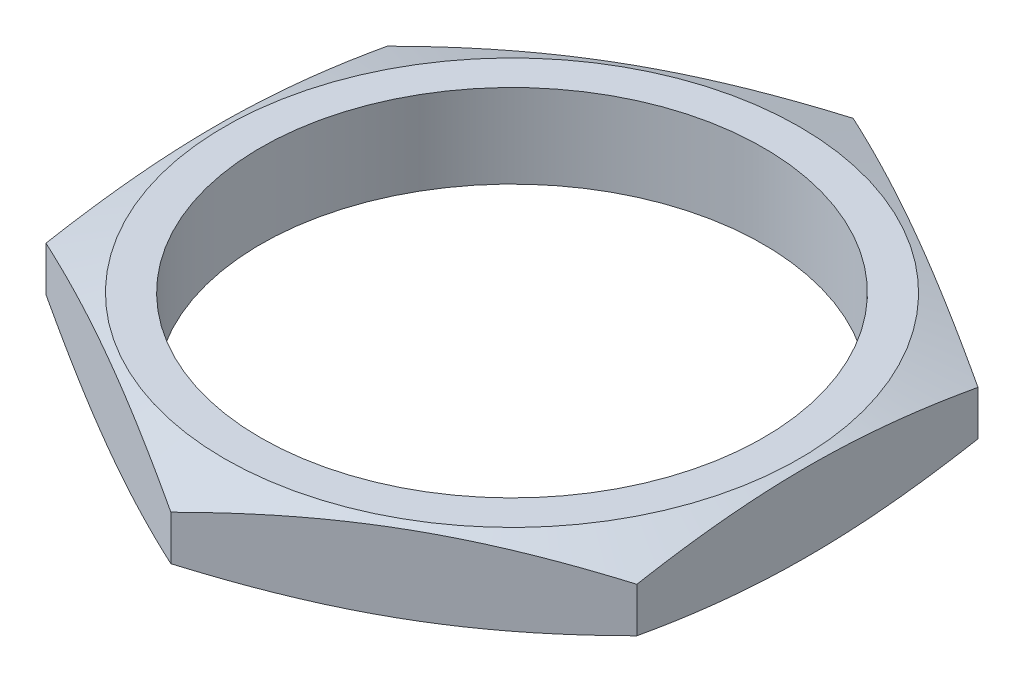
SolidWorks part; units mm, degrees
material "Plain Carbon Steel"
ref_plane "Front Plane" through (0, 0, 0) normal (0, 0, 1) x (1, 0, 0)
ref_plane "Top Plane" through (0, 0, 0) normal (0, 1, 0) x (1, 0, 0)
ref_plane "Right Plane" through (0, 0, 0) normal (1, 0, 0) x (0, 0, -1)
sketch "Sketch1" plane through (0, 0, 0) normal (0, 1, 0) x (1, 0, 0)
  line L0 (0, -55) -> (0, 55) construction
  line L1 (0, -8.0802) -> (6.9977, -4.0401)
  line L2 (6.9977, -4.0401) -> (6.9977, 4.0401)
  line L3 (6.9977, 4.0401) -> (0, 8.0802)
  line L4 (0, 8.0802) -> (-6.9977, 4.0401)
  line L5 (-6.9977, 4.0401) -> (-6.9977, -4.0401)
  line L6 (-6.9977, -4.0401) -> (0, -8.0802)
  circle A0 centre (0, 0) radius 5.9531
  circle A1 centre (0, 0) radius 6.9977 construction
  dimension "D1" = 11.9062
  dimension "D2" = 13.9954
extrude "Boss-Extrude1" add sketch "Sketch1" along normal blind 1.9812
sketch "Sketch2" plane through (0, 0, 0) normal (1, 0, 0) x (0, 0, -1)
  line L0 (-8.0802, 1.519) -> (-6.8102, 1.9812)
  line L1 (-8.0802, 1.9812) -> (-8.0802, 0) construction
  line L2 (-8.0802, 1.9812) -> (-4.0401, 1.9812) construction
  line L3 (-6.8102, 1.9812) -> (-8.0802, 1.9812)
  line L4 (-8.0802, 1.9812) -> (-8.0802, 1.519)
  line L5 (0, 0) -> (0, 1.9812) construction
  line L6 (-4.0401, 1.9812) -> (4.0401, 1.9812) construction
  line L7 (-8.0802, 0.9906) -> (0, 0.9906) construction
  line L8 (-8.0802, 0) -> (-8.0802, 0.4622)
  line L9 (-6.8102, 0) -> (-8.0802, 0)
  line L10 (-8.0802, 0.4622) -> (-6.8102, 0)
  dimension "D1" = 20
  dimension "D2" = 1.27
revolve "Cut-Revolve1" cut sketch "Sketch2" angle 360 about L5
